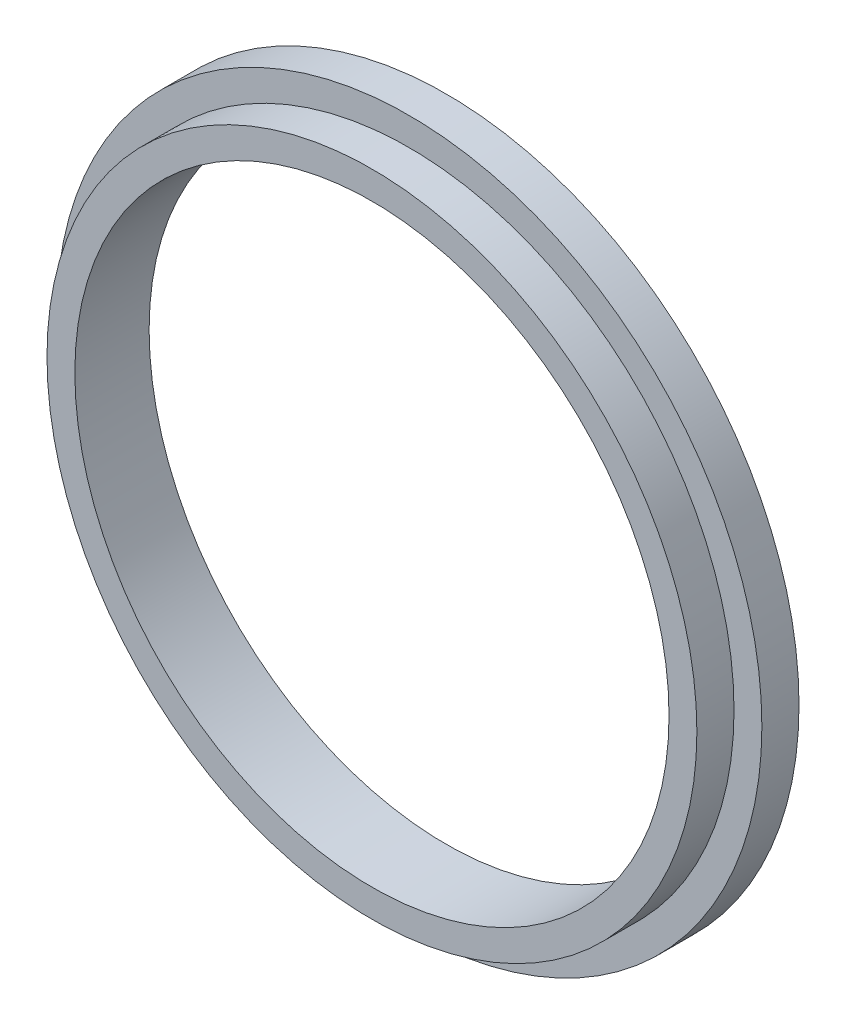
SolidWorks part; units mm, degrees
ref_plane "Alzado" through (0, 0, 0) normal (0, 0, 1) x (1, 0, 0)
ref_plane "Planta" through (0, 0, 0) normal (0, 1, 0) x (1, 0, 0)
ref_plane "Vista lateral" through (0, 0, 0) normal (1, 0, 0) x (0, 0, -1)
sketch "Sketch1" plane through (0, 0, 0) normal (0, 0, 1) x (1, 0, 0)
  circle A0 centre (0, 0) radius 190
  circle A1 centre (0, 0) radius 160
  dimension "D1" = 380
  dimension "D2" = 30
extrude "Boss-Extrude1" add sketch "Sketch1" along normal blind 20
sketch "Sketch2" plane through (0, 0, 20) normal (0, 0, 1) x (1, 0, 0)
  circle A0 centre (0, 0) radius 175
  circle A1 centre (0, 0) radius 190 construction
  circle A2 centre (0, 0) radius 160
  point P6 (0, 0)
  dimension "D1" = 15
  dimension "D2" = 320
extrude "Boss-Extrude2" add sketch "Sketch2" along normal blind 20
sketch "Sketch3" plane through (0, 0, 0) normal (0, 0, 1) x (1, 0, 0)
  line L0 (0, 190) -> (0, -190)
  line L1 (0, 190) -> (195, 190)
  line L2 (195, 190) -> (195, -190)
  line L3 (195, -190) -> (0, -190)
  circle A0 centre (0, 0) radius 190 construction
  dimension "D1" = 195
extrude "Cut-Extrude1" [suppressed] cut sketch "Sketch3" along normal up to next
